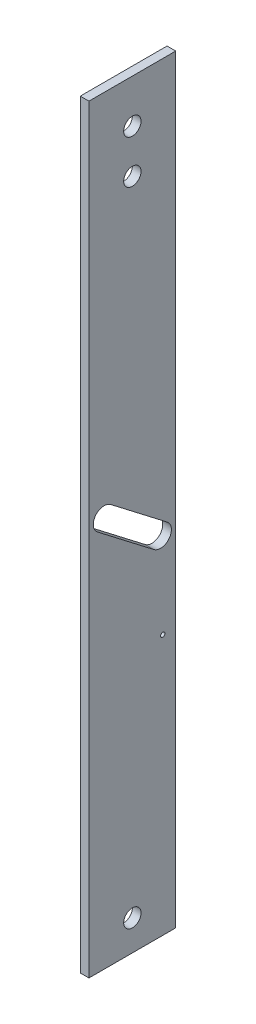
SolidWorks part; units mm, degrees
ref_plane "Front Plane" through (0, 0, 0) normal (0, 0, 1) x (1, 0, 0)
ref_plane "Top Plane" through (0, 0, 0) normal (0, 1, 0) x (1, 0, 0)
ref_plane "Right Plane" through (0, 0, 0) normal (1, 0, 0) x (0, 0, -1)
sketch "Sketch1" plane through (0, 0, 0) normal (1, 0, 0) x (0, 0, -1)
  line L1 (0, 0) -> (20, 0)
  line L2 (0, 0) -> (0, 175)
  line L3 (0, 175) -> (20, 175)
  line L4 (20, 0) -> (20, 175)
  dimension "D1" = 175
  dimension "D2" = 20
extrude "Boss-Extrude1" add sketch "Sketch1" along normal blind 2
sketch "Sketch2" plane through (2, 0, 0) normal (1, 0, 0) x (0, 0, -1)
  line L0 (20, 0) -> (20, 175) construction
  line L1 (0, 0) -> (20, 0) construction
  line L2 (20, 175) -> (0, 175) construction
  line L3 (16.5, 80) -> (3.5, 90) construction
  line L4 (14.9757, 78.0184) -> (1.9757, 88.0184)
  line L5 (18.0243, 81.9816) -> (5.0243, 91.9816)
  line L6 (0, 175) -> (0, 0) construction
  circle A0 centre (10, 7) radius 2
  circle A1 centre (10, 165) radius 2
  circle A2 centre (10, 155) radius 2
  arc A3 (14.9757, 78.0184) -> (18.0243, 81.9816) centre (16.5, 80) ccw
  arc A4 (5.0243, 91.9816) -> (1.9757, 88.0184) centre (3.5, 90) ccw
  circle A5 centre (17, 60) radius 0.5
  point P15 (10, 175)
  point P16 (10, 85)
  point P27 (20, 61.2778)
  dimension "D1" = 4
  dimension "D2" = 4
  dimension "D3" = 4
  dimension "D10" = 80
  dimension "D11" = 90
  dimension "D15" = 1
  dimension "D4" = 10
  dimension "D5" = 10
  dimension "D6" = 10
  dimension "D7" = 7
  dimension "D8" = 10
  dimension "D9" = 20
  dimension "D12" = 3.5
  dimension "D13" = 5
  dimension "D14" = 3.5
  dimension "D16" = 60
  dimension "D17" = 3
extrude "Cut-Extrude1" cut sketch "Sketch2" against normal blind 2
